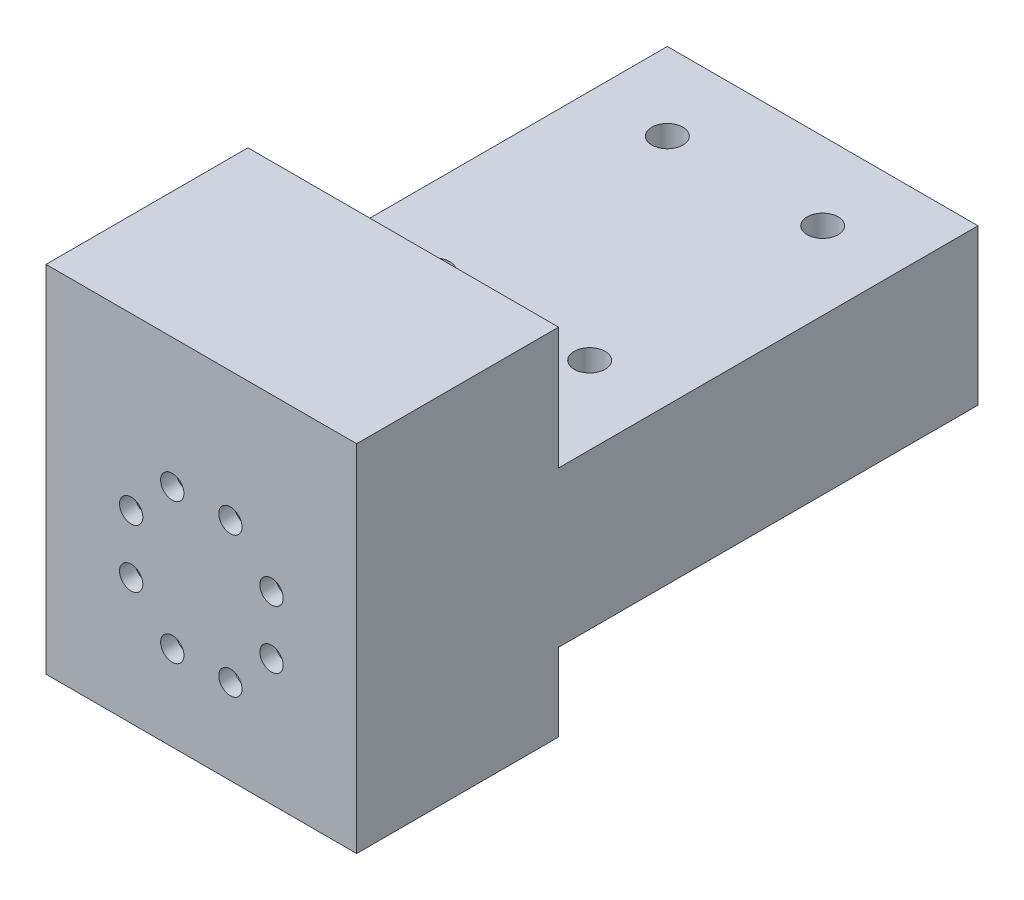
SolidWorks part; units mm, degrees
ref_plane "Alzado" through (0, 0, 0) normal (0, 0, 1) x (1, 0, 0)
ref_plane "Planta" through (0, 0, 0) normal (0, 1, 0) x (1, 0, 0)
ref_plane "Vista lateral" through (0, 0, 0) normal (1, 0, 0) x (0, 0, -1)
sketch "Croquis1" plane through (0, 0, 0) normal (0, 0, 1) x (1, 0, 0)
  line L1 (-20, 20) -> (20, 20)
  line L2 (-20, 20) -> (-20, -20)
  line L3 (-20, -20) -> (20, -20)
  line L4 (20, 20) -> (20, -20)
  line L5 (-20, 20) -> (20, -20) construction
  line L6 (-20, -20) -> (20, 20) construction
  point P0 (0, 0)
extrude "Saliente-Extruir1" add sketch "Croquis1" along normal blind 4
sketch "Croquis2" plane through (0, 0, 4) normal (0, 0, 1) x (1, 0, 0)
  circle A1 centre (-9.0346, -3.7423) radius 1.5
  circle A2 centre (-9.0346, 3.7423) radius 1.5
  circle A3 centre (-3.7423, 9.0346) radius 1.5
  circle A4 centre (3.7423, 9.0346) radius 1.5
  circle A5 centre (9.0346, 3.7423) radius 1.5
  circle A6 centre (9.0346, -3.7423) radius 1.5
  circle A7 centre (3.7423, -9.0346) radius 1.5
  circle A8 centre (-3.7423, -9.0346) radius 1.5
  point P22 (0, 0)
  dimension "D1" = 8
extrude "Cortar-Extruir1" cut sketch "Croquis2" against normal blind 4
sketch "Croquis3" plane through (0, 0, 0) normal (0, 0, -1) x (-1, 0, 0)
  line L0 (-16, -16) -> (-16, -20)
  line L1 (20, 20) -> (-20, 20)
  line L2 (20, 20) -> (20, -20)
  line L3 (20, -20) -> (-20, -20)
  line L4 (-20, 20) -> (-20, -20)
  line L5 (20, 20) -> (-20, -20) construction
  line L6 (20, -20) -> (-20, 20) construction
  line L7 (16, 16) -> (-16, 16)
  line L8 (16, 16) -> (16, -16)
  line L10 (-16, 16) -> (-16, -16)
  line L11 (16, 16) -> (-16, -16) construction
  line L12 (16, -16) -> (-16, 16) construction
  line L13 (-16, -20) -> (16, -20)
  line L14 (16, -20) -> (16, -16)
  point P0 (0, 0)
  point P7 (0, 0)
  line M20 (-20, 20) -> (-20, -20)
  line M21 (-20, -20) -> (20, -20)
  line M22 (20, -20) -> (20, 20)
  line M23 (20, 20) -> (-20, 20)
extrude "Saliente-Extruir2" add sketch "Croquis3" along normal blind 20 contours L14 L3 L0 L10 L7 L8 M22 M23 M20 M21
sketch "Croquis4" plane through (0, 0, -20) normal (0, 0, -1) x (-1, 0, 0)
  line L1 (-20, 20) -> (20, 20)
  line L2 (-20, 20) -> (-20, -20)
  line L3 (-20, -20) -> (20, -20)
  line L4 (20, 20) -> (20, -20)
extrude "Saliente-Extruir3" add sketch "Croquis4" along normal blind 4
sketch "Croquis5" plane through (0, 0, 4) normal (0, 0, 1) x (1, 0, 0)
  line L0 (-6.5, 0) -> (-6.5, -20)
  line L1 (-20, -20) -> (20, -20) construction
  line L2 (-6.5, -20) -> (6.5, -20)
  line L3 (6.5, -20) -> (6.5, 0)
  arc A0 (6.5, 0) -> (-6.5, 0) centre (0, 0) ccw
sketch "Croquis6" plane through (0, 0, 4) normal (0, 0, 1) x (1, 0, 0)
  line L1 (-20, 20) -> (20, 20)
  line L2 (-20, 20) -> (-20, -20)
  line L3 (-20, -20) -> (20, -20)
  line L4 (20, 20) -> (20, -20)
extrude "Cortar-Extruir3" cut sketch "Croquis6" against normal blind 2
sketch "Croquis7" plane through (0, 0, -24) normal (0, 0, -1) x (-1, 0, 0)
  line L0 (20, -20) -> (20, 20) construction
  line L1 (-20, -10) -> (20, -10)
  line L2 (-20, -10) -> (-20, 10)
  line L3 (-20, 10) -> (20, 10)
  line L4 (20, -10) -> (20, 10)
  line L5 (-20, -10) -> (20, 10) construction
  line L6 (-20, 10) -> (20, -10) construction
  point P0 (0, 0)
extrude "Saliente-Extruir4" add sketch "Croquis7" along normal blind 80
sketch "Croquis8" plane through (0, 10, 0) normal (0, 1, 0) x (1, 0, 0)
  circle A7 centre (-10, 38) radius 2
  circle A8 centre (10, 38) radius 2
extrude "Cortar-Extruir4" cut sketch "Croquis8" against normal through all
sketch "Croquis9" plane through (0, 10, 0) normal (0, 1, 0) x (1, 0, 0)
  circle A2 centre (10, 68) radius 2
  circle A4 centre (-10, 68) radius 2
extrude "Cortar-Extruir5" cut sketch "Croquis9" against normal through all
sketch "Croquis11" plane through (0, 0, -104) normal (0, 0, -1) x (-1, 0, 0)
  line L1 (20, 10) -> (-20, 10)
  line L2 (20, 10) -> (20, -10)
  line L3 (20, -10) -> (-20, -10)
  line L4 (-20, 10) -> (-20, -10)
extrude "Cortar-Extruir6" cut sketch "Croquis11" against normal blind 26
sketch "Croquis12" plane through (0, 0, 2) normal (0, 0, 1) x (1, 0, 0)
  circle A0 centre (0, 0) radius 9.779
sketch "Croquis13" plane through (0, 20, 0) normal (0, 1, 0) x (1, 0, 0)
  line L1 (-20, 24) -> (20, 24)
  line L2 (-20, 24) -> (-20, -2)
  line L3 (-20, -2) -> (20, -2)
  line L4 (20, 24) -> (20, -2)
extrude "Saliente-Extruir5" add sketch "Croquis13" along normal blind 5.7
